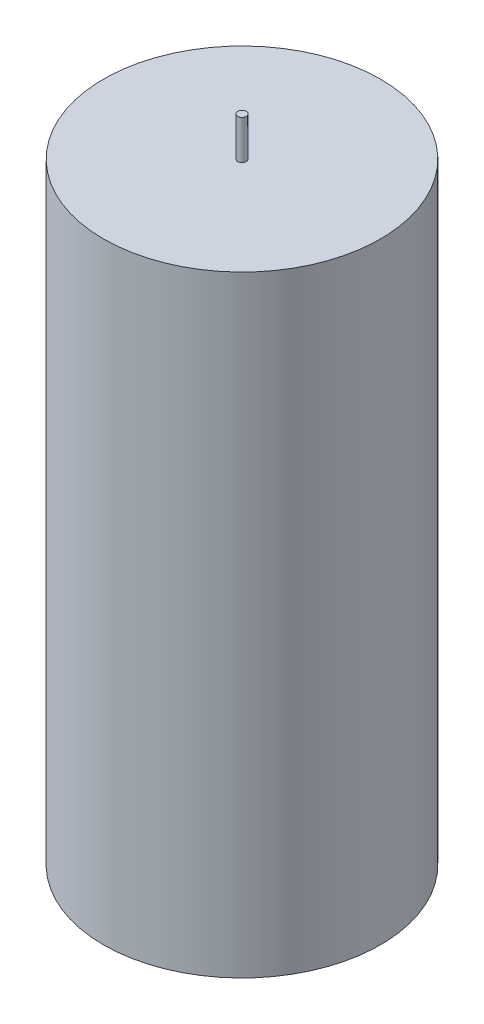
SolidWorks part; units mm, degrees
ref_plane "Alzado" through (0, 0, 0) normal (0, 0, 1) x (1, 0, 0)
ref_plane "Planta" through (0, 0, 0) normal (0, 1, 0) x (1, 0, 0)
ref_plane "Vista lateral" through (0, 0, 0) normal (1, 0, 0) x (0, 0, -1)
sketch "Croquis1" plane through (0, 0, 0) normal (0, 0, 1) x (1, 0, 0)
  line L0 (0, 199.2) -> (2.5, 199.2)
  line L1 (2.5, 199.2) -> (2.5, 176.605)
  line L2 (2.5, 176.605) -> (80, 176.605)
  line L3 (80, 176.605) -> (80, -176.605)
  line L4 (80, 0) -> (0, 0)
  line L5 (0, -199.2) -> (0, 199.2)
  line L6 (337.5089, 0) -> (-200.3399, 0) construction
  line L7 (0, 415.2531) -> (0, -321.1925) construction
  line L8 (2.5, -176.605) -> (80, -176.605)
  line L9 (2.5, -199.2) -> (2.5, -176.605)
  line L10 (0, -199.2) -> (2.5, -199.2)
  dimension "D1" = 80
  dimension "D2" = 2.5
  dimension "D3" = 176.605
  dimension "D4" = 199.2
revolve "Revolución1" add sketch "Croquis1" angle 360 about L7
